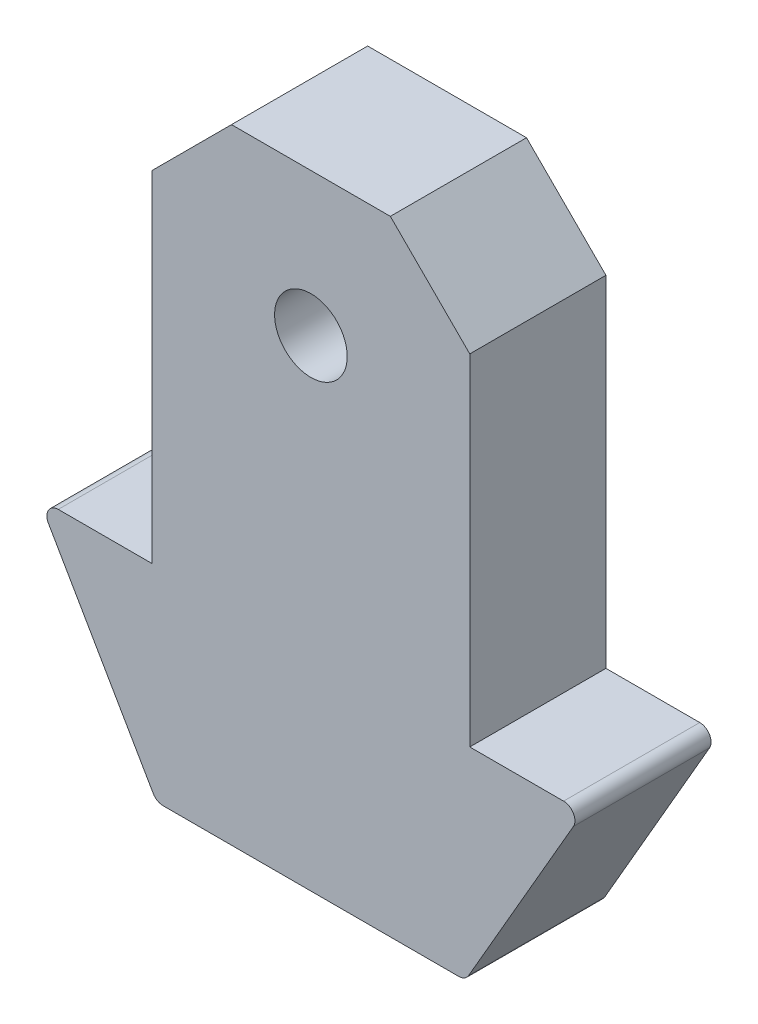
SolidWorks part; units mm, degrees
ref_plane "Front Plane" through (0, 0, 0) normal (0, 0, 1) x (1, 0, 0)
ref_plane "Top Plane" through (0, 0, 0) normal (0, 1, 0) x (1, 0, 0)
ref_plane "Right Plane" through (0, 0, 0) normal (1, 0, 0) x (0, 0, -1)
sketch "Sketch1" plane through (0, 0, 0) normal (0, 0, 1) x (1, 0, 0)
  line L0 (-7, 0) -> (7, 0)
  line L1 (7, 0) -> (7, -18.5)
  line L2 (7, -18.5) -> (12, -18.5)
  line L3 (12, -18.5) -> (6.8038, -27.5)
  line L4 (6.8038, -27.5) -> (-6.8038, -27.5)
  line L5 (-6.8038, -27.5) -> (-12, -18.5)
  line L6 (-12, -18.5) -> (-7, -18.5)
  line L7 (-7, -18.5) -> (-7, 0)
  line L8 (0, 0) -> (0, -27.5) construction
  dimension "D1" = 14
  dimension "D2" = 5
  dimension "D3" = 18.5
  dimension "D4" = 60
  dimension "D5" = 9
extrude "Boss-Extrude1" add sketch "Sketch1" along normal mid plane 6
sketch "Sketch2" plane through (0, 0, 3) normal (0, 0, 1) x (1, 0, 0)
  line L0 (0, 0) -> (0, -6.3) construction
  line L1 (12, -18.5) -> (7, -18.5) construction
  circle A0 centre (0, -6.3) radius 1.6
  dimension "D1" = 3.2
  dimension "D2" = 12.2
extrude "Cut-Extrude1" cut sketch "Sketch2" against normal through all
chamfer "Chamfer1" distance 3.5 angle 45 2 edges at (-7, 0, 0) (7, 0, 0)
fillet "Fillet1" radius 0.5 4 edges at (-6.8038, -27.5, 0) (-12, -18.5, 0) (6.8038, -27.5, 0) (12, -18.5, 0)
